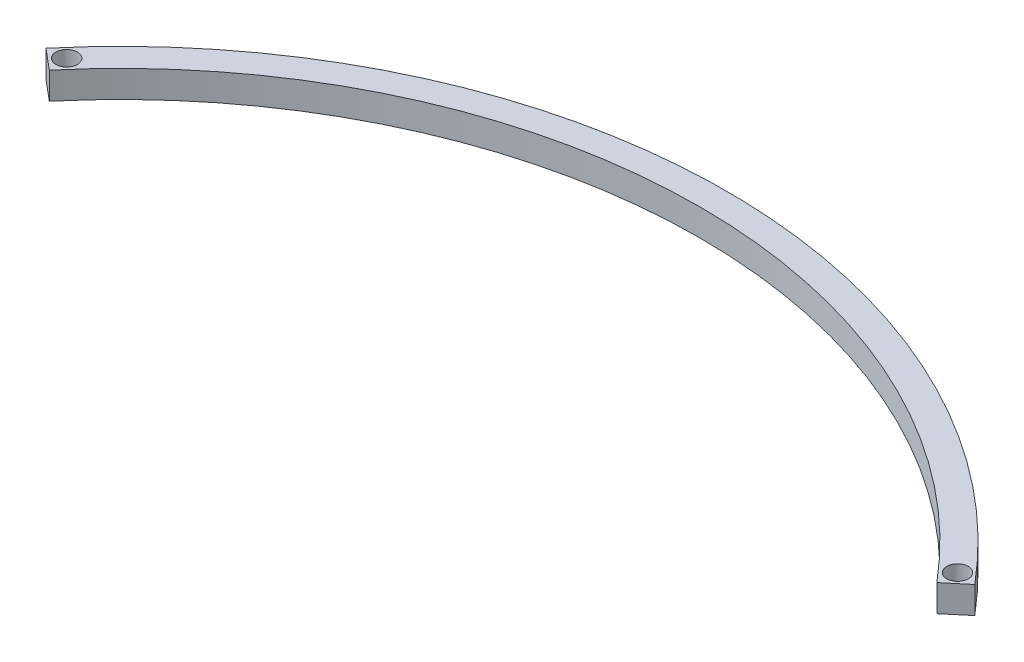
SolidWorks part; units mm, degrees
ref_plane "Front Plane" through (0, 0, 0) normal (0, 0, 1) x (1, 0, 0)
ref_plane "Top Plane" through (0, 0, 0) normal (0, 1, 0) x (1, 0, 0)
ref_plane "Right Plane" through (0, 0, 0) normal (1, 0, 0) x (0, 0, -1)
sketch "Sketch1" plane through (0, 0, 0) normal (0, 1, 0) x (1, 0, 0)
  line L0 (-172.36, 144.6272) -> (-164.6996, 138.1993)
  line L1 (172.36, 144.6272) -> (164.6996, 138.1993)
  line L2 (-164.6996, 138.1993) -> (0, 0) construction
  line L3 (0, 0) -> (164.6996, 138.1993) construction
  line L4 (0, 0) -> (0, 215) construction
  line L5 (-168.5298, 141.4133) -> (-165.3158, 145.2435) construction
  arc A0 (-172.36, 144.6272) -> (172.36, 144.6272) centre (0, 0) cw
  arc A1 (-164.6996, 138.1993) -> (164.6996, 138.1993) centre (0, 0) cw
  circle A2 centre (-165.3158, 145.2435) radius 4
  circle A4 centre (165.3158, 145.2435) radius 4
  dimension "D1" = 10
  dimension "D2" = 215
  dimension "D4" = 8
  dimension "D3" = 100
  dimension "D5" = 5
extrude "Boss-Extrude1" add sketch "Sketch1" along normal mid plane 10
